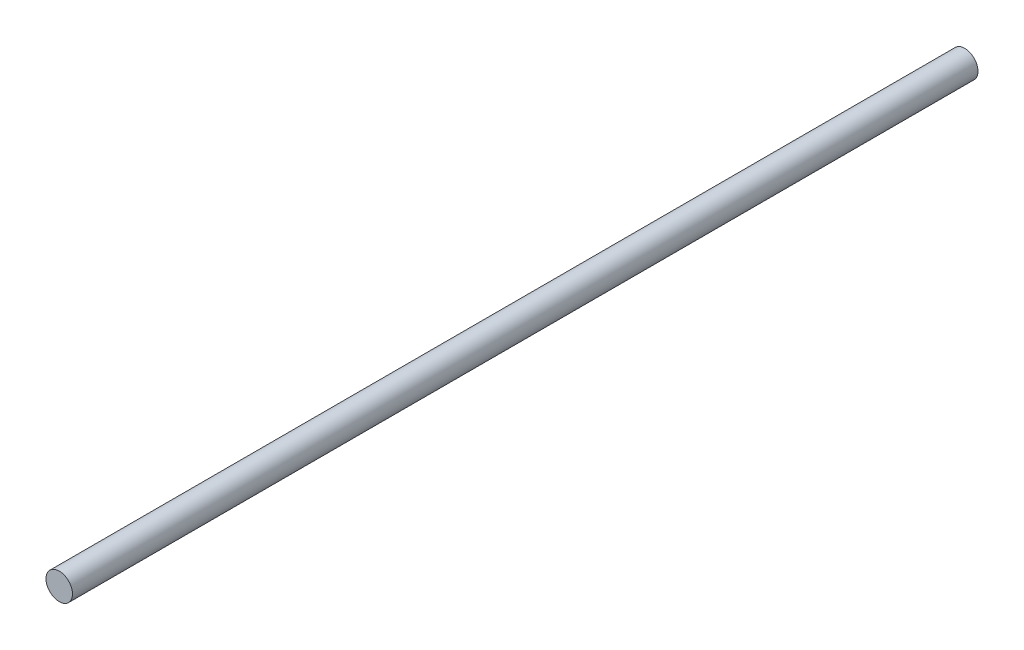
SolidWorks part; units mm, degrees
ref_plane "Front" through (0, 0, 0) normal (0, 0, 1) x (1, 0, 0)
ref_plane "Top" through (0, 0, 0) normal (0, 1, 0) x (1, 0, 0)
ref_plane "Right" through (0, 0, 0) normal (1, 0, 0) x (0, 0, -1)
sketch "Sketch2" plane through (0, 0, 0) normal (0, 0, 1) x (1, 0, 0)
  circle A0 centre (0, 0) radius 6
  dimension "D1" = 12
extrude "Boss-Extrude1" add sketch "Sketch2" along normal blind 410
